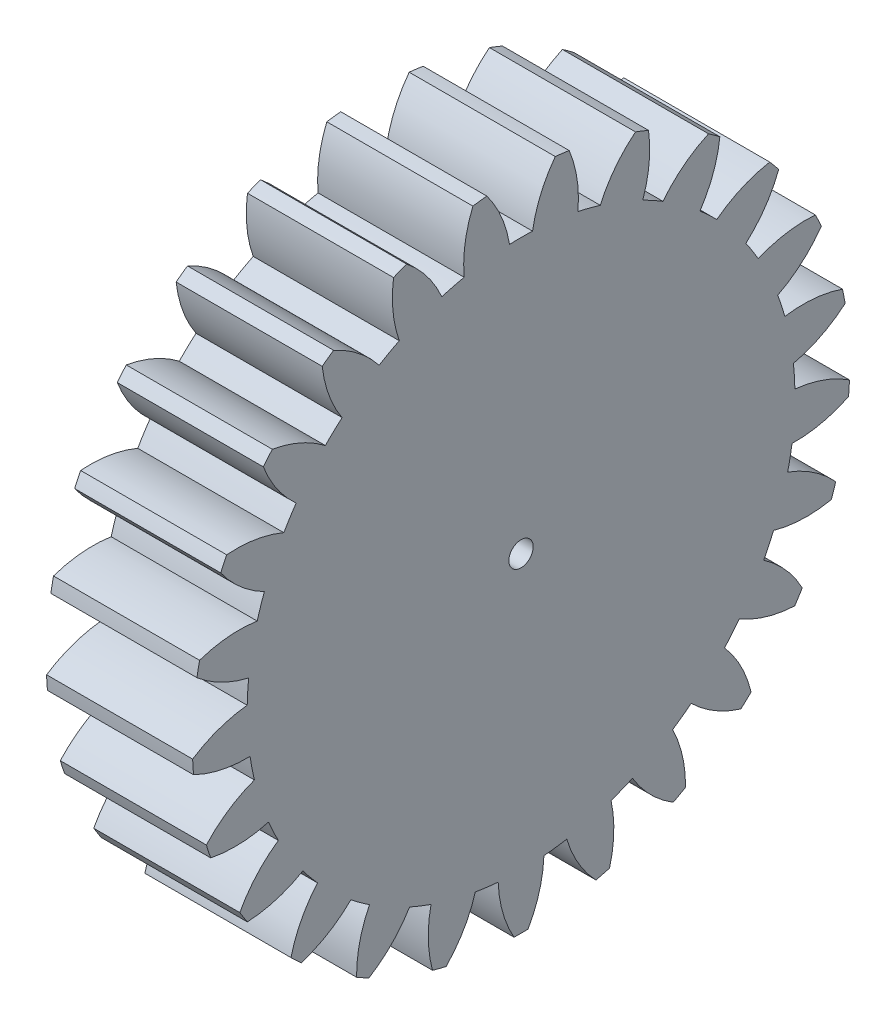
SolidWorks part; units mm, degrees
ref_plane "Plane1" through (0, 0, 0) normal (0, 0, 1) x (1, 0, 0)
ref_plane "Plane2" through (0, 0, 0) normal (0, 1, 0) x (1, 0, 0)
ref_plane "Plane3" through (0, 0, 0) normal (1, 0, 0) x (0, 0, -1)
other "Configuration Table"
sketch "HoldingSke" plane through (0, 0, 0) normal (0, 1, 0) x (1, 0, 0)
  line L0 (0, 0) -> (0.4532, -0.2113)
  line L1 (-15, 0) -> (100, 0) construction
  line L2 (0, 0) -> (-2.1039, 2.3779)
  line L3 (0, 0) -> (-11.863, 4.5341)
  line L4 (0, 0) -> (7.8269, 3.6497)
  line L5 (0, 0) -> (-46.8476, -17.4728)
  line L6 (0, 0) -> (-9.9476, -6.7116)
  line L7 (-2.1039, 2.3779) -> (8.6586, 51.2059)
  line L8 (-76.2, 54.61) -> (-75.9, 54.61)
  line L9 (-71.009, 38.7566) -> (-53.1078, 45.2721)
  line L10 (-76.2, 71.12) -> (104.1128, 71.12)
  line L11 (0, 0) -> (-12, 0)
  line L12 (-76.2, 101.6) -> (-76.133, 101.6)
  line L13 (24.9733, 27.94) -> (52.9518, 28.4284)
  line L14 (24.9733, 27.94) -> (24.9743, 27.94)
  line L15 (24.9733, 27.94) -> (100.4006, 29.5858)
  line L16 (-63.627, -2) -> (-12.827, -2)
  circle A0 centre (0, 0) radius 1
  circle A1 centre (0, 0) radius 22.499
  circle A2 centre (0, 0) radius 37.5
  circle A3 centre (0, 0) radius 1
  dimension "MHD" = 44.998
  dimension "Hub_dia" = 75
  dimension "Bore" = 2
  dimension "MBD" = 2
  dimension "Num_teeth" = 25
  dimension "Pitch" = 0.5
  dimension "Overall_len" = 50
  dimension "Show_teeth" = 25
  dimension "Thickness" = 12
  dimension "OAL" = 50.0001
  dimension "T_dim" = 0.3
  dimension "Ap" = 20
  dimension "H" = 19.05
  dimension "Pitch_radius" = 180.3128
  dimension "Width" = 12
  dimension "Backlash" = 0.067
  dimension "Addendum_fac" = 1
  dimension "Dedendum_fac" = 1.25
  dimension "Clearance_fac" = 0.25
  dimension "Dedendum_add" = 0.001
  dimension "Module" = 2
sketch "BasProSke" plane through (0, 0, 0) normal (0, 1, 0) x (1, 0, 0)
  line L0 (-10, 0) -> (60, 0) construction
  line L1 (0, 0) -> (0, 27)
  line L2 (0, 0) -> (12, 0)
  line L3 (12, 0) -> (12, 27)
  line L4 (12, 27) -> (0, 27)
  dimension "Thickness" = 12
  dimension "Diameter" = 54
revolve "Base-Revolve" add sketch "BasProSke" angle 360 about L0
sketch "TooCutSke" plane through (0, 0, 0) normal (1, 0, 0) x (0, 0, -1)
  line L1 (0, 0) -> (0, 107) construction
  line L2 (0, 0) -> (-1.687, 24.943) construction
  line L3 (0, 0) -> (-6.2561, 49.5219) construction
  line L4 (-1.687, 24.943) -> (-3.128, 24.761) construction
  arc A0 (0.9462, 22.4791) -> (-0.9462, 22.4791) centre (0, 0) ccw
  arc A1 (2.8295, 26.8769) -> (-2.8295, 26.8769) centre (0, 0) ccw
  circle A2 centre (0, 0) radius 25 construction
  circle A3 centre (0, 0) radius 23.4923 construction
  arc A4 (-0.9462, 22.4791) -> (-2.8295, 26.8769) centre (-10.8135, 20.8556) ccw
  arc A5 (2.8295, 26.8769) -> (0.9462, 22.4791) centre (10.8135, 20.8556) ccw
  dimension "Root_dia" = 44.998
  dimension "Overcut_dia" = 54.0508
  dimension "Pitch_dia" = 50
  dimension "Base_dia" = 46.9846
  dimension "Flank_rad" = 10
  dimension "Half_ang" = 7.2
  dimension "Half_CT" = 1.4525
extrude "ToothCut" cut sketch "TooCutSke" along normal through all
fillet "Breaks" [suppressed] radius 0.04
fillet "RootFillets" [suppressed] radius 0.501
pattern_circular "TeethCuts" count 25 every 14.4 about axis through (-10, 0, 0) along (1, 0, 0) of "ToothCut", "RootFillets", "Breaks"
sketch "HubNeaOneSke" plane through (0, 0, 0) normal (-1, 0, 0) x (0, 0, 1)
  circle A0 centre (0, 0) radius 22.499
  dimension "Diameter" = 44.998
extrude "HubNearOne" [suppressed] add sketch "HubNeaOneSke" along normal blind 38.0001
sketch "HubNeaBotSke" plane through (0, 0, 0) normal (-1, 0, 0) x (0, 0, 1)
  circle A0 centre (0, 0) radius 22.499
  dimension "Diameter" = 44.998
extrude "HubNearBoth" [suppressed] add sketch "HubNeaBotSke" along normal blind 19
ref_plane "FarPln" through (12, 0, 0) normal (1, 0, 0) x (0, 0, -1)
sketch "HubFarSke" plane through (12, 0, 0) normal (1, 0, 0) x (0, 0, -1)
  circle A0 centre (0, 0) radius 22.499
  dimension "Diameter" = 44.998
extrude "HubFar" [suppressed] add sketch "HubFarSke" along normal blind 19
sketch "BorSke" plane through (0, 0, 0) normal (1, 0, 0) x (0, 0, -1)
  circle A0 centre (0, 0) radius 1
  dimension "Diameter" = 2
extrude "Bore" cut sketch "BorSke" along normal mid plane 100.0001
sketch "KeySke" plane through (0, 0, 0) normal (1, 0, 0) x (0, 0, -1)
  line L0 (-0.4, 0) -> (-0.4, 1.3)
  line L1 (-0.4, 1.3) -> (0.4, 1.3)
  line L2 (0.4, 1.3) -> (0.4, 0)
  line L3 (0, 0) -> (0, 34) construction
  line L4 (-0.4, 0) -> (0.4, 0)
  dimension "Offset" = 1.3
  dimension "Width" = 0.8
extrude "Keyway" [suppressed] cut sketch "KeySke" along normal mid plane 100.0001
pattern_circular "Keyway2" [suppressed] count 2 every 90 about axis through (-10, 0, 0) along (1, 0, 0)
equation "' \"Module@HoldingSke\" = 6.35"
equation "' \"Num_teeth@HoldingSke\" = 12"
equation "' \"Ap@HoldingSke\" =  20"
equation "' \"Ap@HoldingSke\" = 20"
equation "' \"Width@HoldingSke\" = 0.5 * 25.4"
equation "' \"Hub_dia@HoldingSke\"= 1 * 25.4"
equation "' \"Hub_dia@HoldingSke\" = 1 * 25.4"
equation "' \"Overall_len@HoldingSke\" = 1.0 * 25.4"
equation "' \"Bore@HoldingSke\" = 0.75 * 25.4"
equation "' \"T_dim@HoldingSke\" = 0.1 * 25.4"
equation "' \"Width@KeySke\" = 0.25 * 25.4"
equation "' \"Show_teeth@HoldingSke\" = 13"
equation "' \"Backlash@HoldingSke\" = 0.009 * 25.4"
equation "' \"Addendum_fac@HoldingSke\" = 1.0"
equation "' \"Dedendum_fac@HoldingSke\" = 1.25"
equation "' \"Dedendum_add@HoldingSke\" = 0.00005 * 25.4"
equation "' \"Clearance_fac@HoldingSke\" = 0.25"
equation "\"Pitch@HoldingSke\" = 1 / \"Module@HoldingSke\""
equation "\"Overcut_dia@TooCutSke\" = (\"Num_teeth@HoldingSke\" + 2 * \"Addendum_fac@HoldingSke\") / \"Pitch@HoldingSke\" + 0.002 * 25.4"
equation "\"Pitch_dia@TooCutSke\" = \"Num_teeth@HoldingSke\" / \"Pitch@HoldingSke\""
equation "\"Base_dia@TooCutSke\" = \"Num_teeth@HoldingSke\" / \"Pitch@HoldingSke\" * cos((\"Ap@HoldingSke\"  * 3.14159265 / 180))"
equation "\"Root_dia@TooCutSke\" = (\"Num_teeth@HoldingSke\" + 2) / \"Pitch@HoldingSke\" - 2 * (\"Addendum_fac@HoldingSke\" + \"Dedendum_fac@HoldingSke\") / \"Pitch@HoldingSke\" - \"Dedendum_add@HoldingSke\" * 2"
equation "\"Half_ang@TooCutSke\" = 180 / \"Num_teeth@HoldingSke\""
equation "\"Half_CT@TooCutSke\" = \"Num_teeth@HoldingSke\" / \"Pitch@HoldingSke\" * sin((3.14159265 / 2 / \"Num_teeth@HoldingSke\")) / 2 - 7 * \"Backlash@HoldingSke\" / 4"
equation "\"Flank_rad@TooCutSke\" = \"Num_teeth@HoldingSke\" / \"Pitch@HoldingSke\" / 5"
equation "\"Radius@RootFillets\" = \"Clearance_fac@HoldingSke\" / \"Pitch@HoldingSke\" + \"Dedendum_add@HoldingSke\""
equation "\"Break_rad@Breaks\" = 0.02 / \"Pitch@HoldingSke\""
equation "\"Thickness@HoldingSke\" = \"Width@HoldingSke\""
equation "\"OAL@HoldingSke\" = \"Thickness@HoldingSke\""
equation "\"MHD@HoldingSke\" = (\"Num_teeth@HoldingSke\" + 2) / \"Pitch@HoldingSke\" - 2 * (\"Addendum_fac@HoldingSke\" + \"Dedendum_fac@HoldingSke\")  / \"Pitch@HoldingSke\" - \"Dedendum_add@HoldingSke\" * 2"
equation "\"MBD@HoldingSke\" = (\"Num_teeth@HoldingSke\" + 2) / \"Pitch@HoldingSke\" - 2 * (\"Addendum_fac@HoldingSke\" + \"Dedendum_fac@HoldingSke\")  / \"Pitch@HoldingSke\" - \"Dedendum_add@HoldingSke\" * 2 - 0.002 * 25.4"
equation "\"MHD@HoldingSke\" = ((sgn( \"MHD@HoldingSke\" - \"Hub_dia@HoldingSke\" )-1)*( \"MHD@HoldingSke\" - \"Hub_dia@HoldingSke\" ))/-2+ \"Hub_dia@HoldingSke\""
equation "\"MBD@HoldingSke\" = ((sgn( \"MBD@HoldingSke\" - \"Bore@HoldingSke\" )-1)*( \"MBD@HoldingSke\" - \"Bore@HoldingSke\" ))/-2+ \"Bore@HoldingSke\""
equation "\"OAL@HoldingSke\" = ((sgn( \"OAL@HoldingSke\" - \"Overall_len@HoldingSke\" )+1)*( \"OAL@HoldingSke\" - \"Overall_len@HoldingSke\" ))/2 + \"Overall_len@HoldingSke\" + 0.000002 * 25.4"
equation "\"Num_teeth@TeethCuts\" = int( \"Show_teeth@HoldingSke\" ) + 1"
equation "\"Num_teeth@TeethCuts\" = ((sgn( \"Num_teeth@TeethCuts\" - \"Num_teeth@HoldingSke\" )-1)*( \"Num_teeth@TeethCuts\" - \"Num_teeth@HoldingSke\" ))/-2+ \"Num_teeth@HoldingSke\""
equation "\"Num_teeth@TeethCuts\" = ((sgn( \"Num_teeth@TeethCuts\" - 2.0)+1)*( \"Num_teeth@TeethCuts\" - 2.0))/2 +2.0"
equation "\"Angle@TeethCuts\" = 360.0 / \"Num_teeth@HoldingSke\""
equation "\"Diameter@BasProSke\" = (\"Num_teeth@HoldingSke\" + 2 * \"Addendum_fac@HoldingSke\") / \"Pitch@HoldingSke\""
equation "\"Thickness@BasProSke\"  = \"Thickness@HoldingSke\""
equation "' \"Fillet_rad@BasProSke\" =  \"Thickness@HoldingSke\" * 0.05"
equation "' \"Fillet_rad@BasProSke\" = \"Thickness@HoldingSke\" * 0.05"
equation "\"MHD@HoldingSke\" = ((sgn( \"MHD@HoldingSke\" - \"Root_dia@TooCutSke\" )-1)*( \"MHD@HoldingSke\" - \"Root_dia@TooCutSke\" ))/-2+ \"Root_dia@TooCutSke\""
equation "\"Diameter@HubNeaOneSke\" = \"MHD@HoldingSke\""
equation "\"Length@HubNearOne\" = \"OAL@HoldingSke\" - \"Thickness@BasProSke\""
equation "\"Diameter@HubNeaBotSke\" = \"MHD@HoldingSke\""
equation "\"Length@HubNearBoth\" = ( \"OAL@HoldingSke\" - \"Thickness@BasProSke\" ) / 2.0"
equation "\"Thickness@FarPln\" = \"Thickness@BasProSke\""
equation "\"Diameter@HubFarSke\" = \"MHD@HoldingSke\""
equation "\"Length@HubFar\" = ( \"OAL@HoldingSke\" - \"Thickness@BasProSke\" ) / 2.0"
equation "\"Diameter@BorSke\" = \"MBD@HoldingSke\""
equation "\"D1@Bore\" = \"OAL@HoldingSke\" * 2.0"
equation "\"D1@Keyway\" = \"OAL@HoldingSke\" * 2.0"
equation "\"Offset@KeySke\" = \"T_dim@HoldingSke\" + \"MBD@HoldingSke\" / 2.0"
